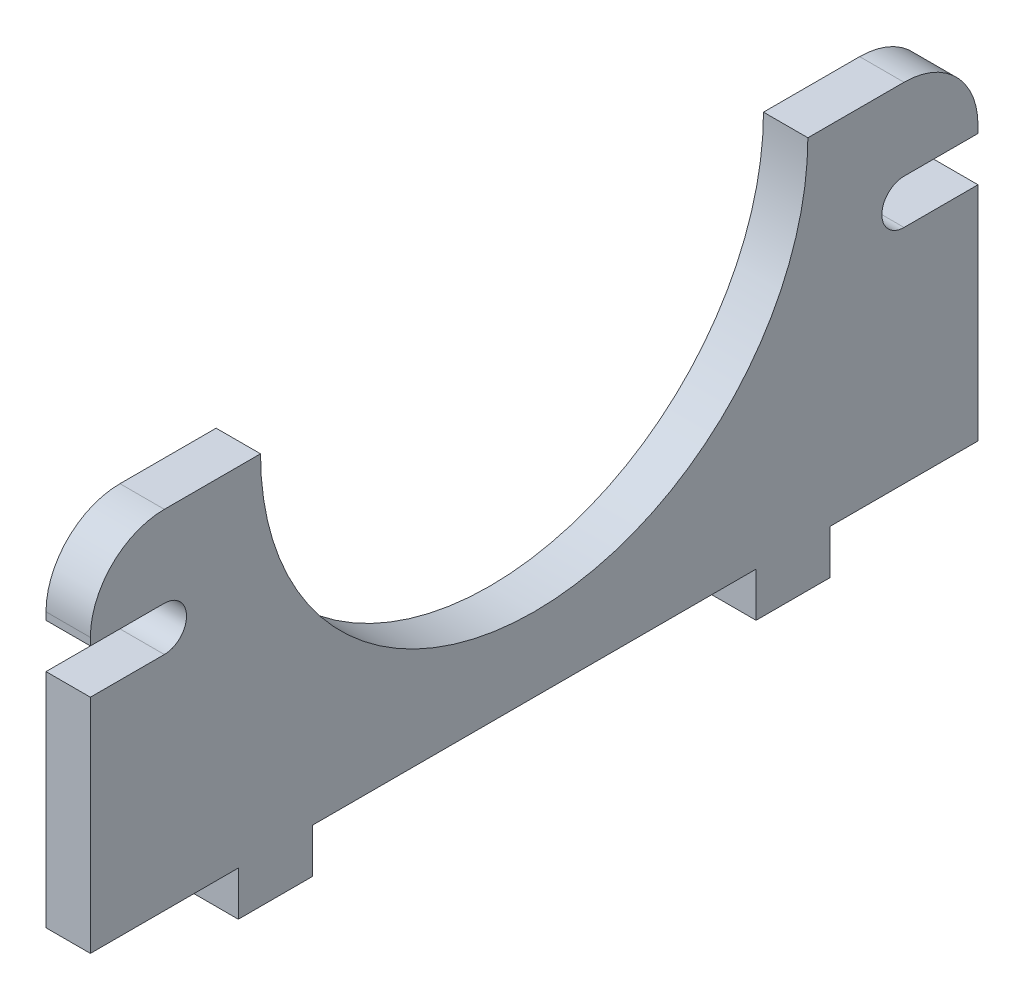
SolidWorks part; units mm, degrees
ref_plane "Front Plane" through (0, 0, 0) normal (0, 0, 1) x (1, 0, 0)
ref_plane "Top Plane" through (0, 0, 0) normal (0, 1, 0) x (1, 0, 0)
ref_plane "Right Plane" through (0, 0, 0) normal (1, 0, 0) x (0, 0, -1)
ref_plane "Plane2" through (0, -2, 0) normal (0, 1, 0) x (1, 0, 0)
sketch "Sketch1" plane through (0, 0, 0) normal (1, 0, 0) x (0, 0, -1)
  line L0 (-18.5, 11.75) -> (-30, 11.75)
  line L1 (30, -11.75) -> (-30, -11.75)
  line L2 (30, -11.75) -> (30, 11.75)
  line L3 (30, 11.75) -> (18.5, 11.75)
  line L4 (-30, -11.75) -> (-30, 11.75)
  line L5 (30, -11.75) -> (-30, 11.75) construction
  line L6 (30, 11.75) -> (-30, -11.75) construction
  arc A0 (-18.5, 11.75) -> (18.5, 11.75) centre (0, 11.75) ccw
  point P0 (0, 0)
  dimension "D1" = 37
  dimension "D2" = 60
  dimension "D3" = 23.5
extrude "Boss-Extrude1" add sketch "Sketch1" along normal blind 3
sketch "Sketch2" plane through (3, 0, 0) normal (1, 0, 0) x (0, 0, -1)
  line L0 (-30, -11.75) -> (30, -11.75) construction
  line L6 (-30, 11.75) -> (-30, -11.75) construction
  line L8 (-25, 6.25) -> (-30, 6.25)
  line L10 (-25, 3.25) -> (-30, 3.25)
  line L11 (-30, 6.25) -> (-30, 3.25)
  arc A0 (-25, 3.25) -> (-25, 6.25) centre (-25, 4.75) ccw
  point P0 (-25, 4.75)
  dimension "D1" = 5
  dimension "D3" = 1.5
  dimension "D2" = 15
extrude "Cut-Extrude2" cut sketch "Sketch2" against normal through all
mirror "Mirror2" about plane through (0, 0, 0) normal (0, 0, 1) of "Cut-Extrude2"
fillet "Fillet2" radius 5 2 edges at (1.5, 11.75, 30) (1.5, 11.75, -30)
sketch "Sketch3" plane through (0, -11.75, 0) normal (0, -1, 0) x (1, 0, 0)
  line L0 (0, 30) -> (0, -30) construction
  line L1 (0, -20) -> (3, -20)
  line L2 (0, -20) -> (0, -15)
  line L3 (0, -15) -> (3, -15)
  line L4 (3, -20) -> (3, -15)
  line L5 (3, 30) -> (3, -30) construction
  line L6 (3, -30) -> (0, -30) construction
  dimension "D1" = 10
  dimension "D2" = 5
extrude "Boss-Extrude2" add sketch "Sketch3" along normal blind 3
mirror "Mirror3" about plane through (0, 0, 0) normal (0, 0, 1) of "Boss-Extrude2"
